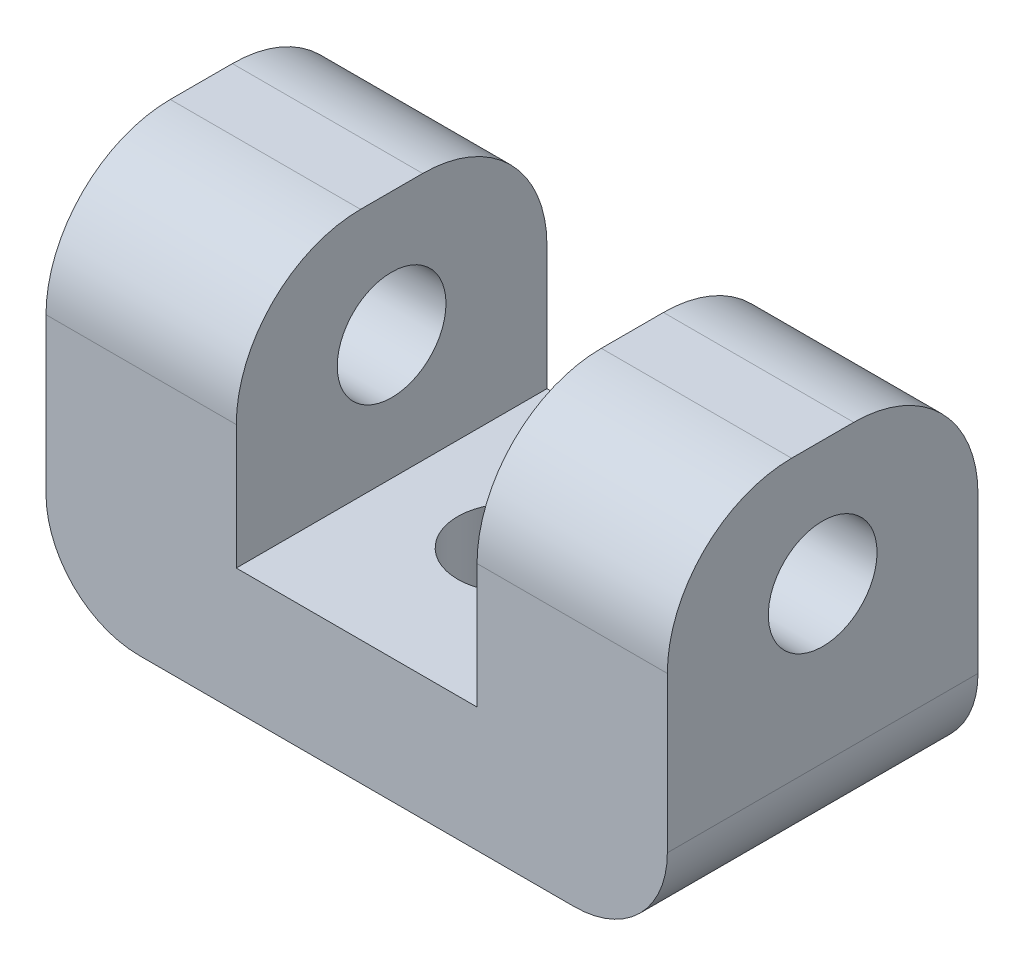
SolidWorks part; units mm, degrees
ref_plane "Front Plane" through (0, 0, 0) normal (0, 0, 1) x (1, 0, 0)
ref_plane "Top Plane" through (0, 0, 0) normal (0, 1, 0) x (1, 0, 0)
ref_plane "Right Plane" through (0, 0, 0) normal (1, 0, 0) x (0, 0, -1)
sketch "Sketch1" plane through (0, 0, 0) normal (0, 1, 0) x (1, 0, 0)
  line L1 (-10, 5) -> (10, 5)
  line L2 (-10, 5) -> (-10, -5)
  line L3 (-10, -5) -> (10, -5)
  line L4 (10, 5) -> (10, -5)
  line L5 (-10, 5) -> (10, -5) construction
  line L6 (-10, -5) -> (10, 5) construction
  point P0 (0, 0)
  dimension "D1" = 20
  dimension "D2" = 10
extrude "Boss-Extrude1" add sketch "Sketch1" along normal blind 12
sketch "Sketch2" plane through (0, 12, 0) normal (0, 1, 0) x (1, 0, 0)
  line L0 (10, 5) -> (-10, 5) construction
  line L1 (-3.8749, 5) -> (3.8749, 5)
  line L2 (-3.8749, 5) -> (-3.8749, -5)
  line L3 (-3.8749, -5) -> (3.8749, -5)
  line L4 (3.8749, 5) -> (3.8749, -5)
  line L5 (-10, -5) -> (10, -5) construction
  line L6 (0, 0) -> (0, -5) construction
extrude "Cut-Extrude1" cut sketch "Sketch2" against normal blind 8
fillet "Fillet1" radius 4 4 edges at (-6.9375, 12, 5) (-6.9375, 12, -5) (6.9375, 12, -5) (6.9375, 12, 5)
sketch "Sketch3" plane through (10, 0, 0) normal (1, 0, 0) x (0, 0, -1)
  line L0 (0, 12) -> (0, 8) construction
  line L1 (-1, 12) -> (1, 12) construction
  circle A0 centre (0, 8) radius 1.75
  dimension "D2" = 3.5
  dimension "D1" = 4
extrude "Cut-Extrude2" cut sketch "Sketch3" against normal through all
fillet "Fillet2" radius 3 2 edges at (10, 0, 0) (-10, 0, 0)
sketch "Sketch4" plane through (0, 4, 0) normal (0, 1, 0) x (1, 0, 0)
  circle A0 centre (0, 0) radius 1.75
  dimension "D1" = 3.5
extrude "Cut-Extrude3" cut sketch "Sketch4" against normal through all
